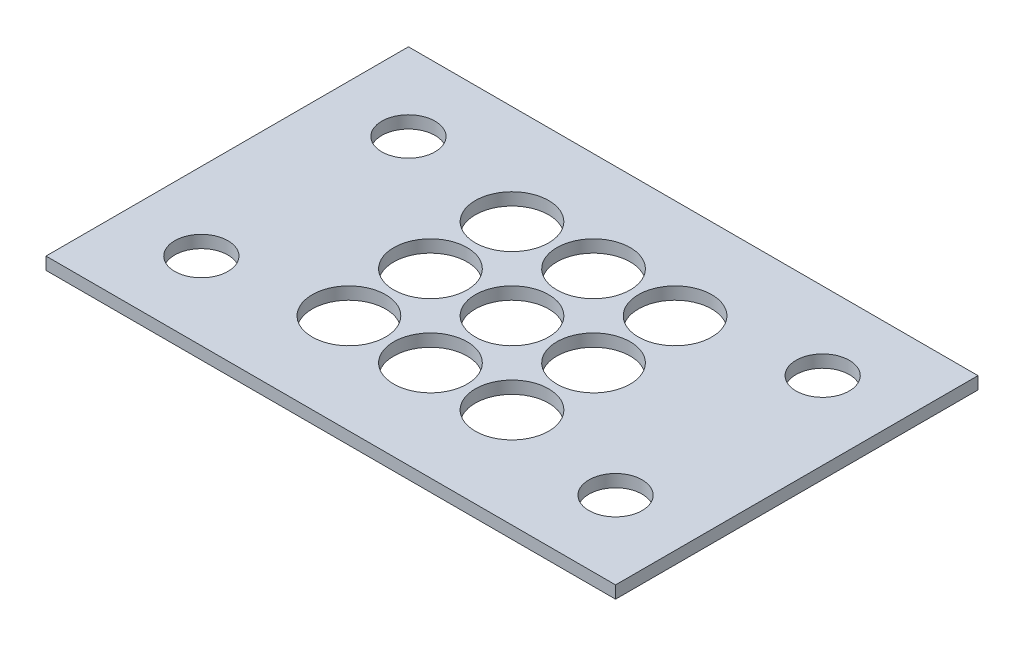
SolidWorks part; units mm, degrees
ref_plane "Front Plane" through (0, 0, 0) normal (0, 0, 1) x (1, 0, 0)
ref_plane "Top Plane" through (0, 0, 0) normal (0, 1, 0) x (1, 0, 0)
ref_plane "Right Plane" through (0, 0, 0) normal (1, 0, 0) x (0, 0, -1)
sketch "Sketch1" plane through (0, 0, 0) normal (0, 1, 0) x (1, 0, 0)
  line L0 (9.525, 34.925) -> (0, 34.925) construction
  line L1 (0, 0) -> (69.85, 0)
  line L2 (0, 0) -> (0, 44.45)
  line L3 (0, 44.45) -> (69.85, 44.45)
  line L4 (69.85, 0) -> (69.85, 44.45)
  line L5 (9.525, 34.925) -> (60.325, 34.925) construction
  line L6 (9.525, 34.925) -> (9.525, 9.525) construction
  line L7 (9.525, 9.525) -> (60.325, 9.525) construction
  line L8 (60.325, 34.925) -> (60.325, 9.525) construction
  line L9 (9.525, 34.925) -> (9.525, 44.45) construction
  circle A0 centre (9.525, 34.925) radius 3.2639
  circle A1 centre (60.325, 34.925) radius 3.2639
  circle A2 centre (9.525, 9.525) radius 3.2639
  circle A3 centre (60.325, 9.525) radius 3.2639
  circle A4 centre (34.925, 22.225) radius 4.5
  circle A5 centre (44.925, 22.225) radius 4.5
  circle A6 centre (44.925, 32.225) radius 4.5
  circle A7 centre (34.925, 32.225) radius 4.5
  circle A8 centre (44.925, 22.225) radius 4.5
  circle A9 centre (44.925, 12.225) radius 4.5
  circle A10 centre (34.925, 12.225) radius 4.5
  circle A11 centre (24.925, 22.225) radius 4.5
  circle A12 centre (24.925, 32.225) radius 4.5
  circle A13 centre (34.925, 32.225) radius 4.5
  circle A14 centre (24.925, 22.225) radius 4.5
  circle A15 centre (24.925, 12.225) radius 4.5
  circle A16 centre (34.925, 12.225) radius 4.5
  point P13 (34.925, 34.925)
  point P14 (34.925, 44.45)
  point P19 (0, 0)
  point P20 (69.85, 22.225)
  point P22 (0, 0)
  point P46 (30.0619, 25.5894)
  point P47 (35.5752, 26.2452)
  dimension "D5" = 6.5278
  dimension "D6" = 9
  dimension "D1" = 69.85
  dimension "D2" = 44.45
  dimension "D3" = 50.8
  dimension "D4" = 25.4
  dimension "D15" = 10
  dimension "D16" = 10
  dimension "D17" = 10
  dimension "D18" = 10
  dimension "D19" = 10
  dimension "D20" = 10
  dimension "D21" = 10
  dimension "D22" = 10
  dimension "D7" = 2
  dimension "D8" = 2
  dimension "D9" = 2
  dimension "D10" = 2
  dimension "D11" = 2
  dimension "D12" = 2
  dimension "D13" = 2
  dimension "D14" = 2
extrude "Boss-Extrude1" add sketch "Sketch1" along normal blind 1.524 contours L1 L4 L3 L2 A15 A12 A11 A10 A9 A7 A6 A5 A4 A3 A2 A1 A0
